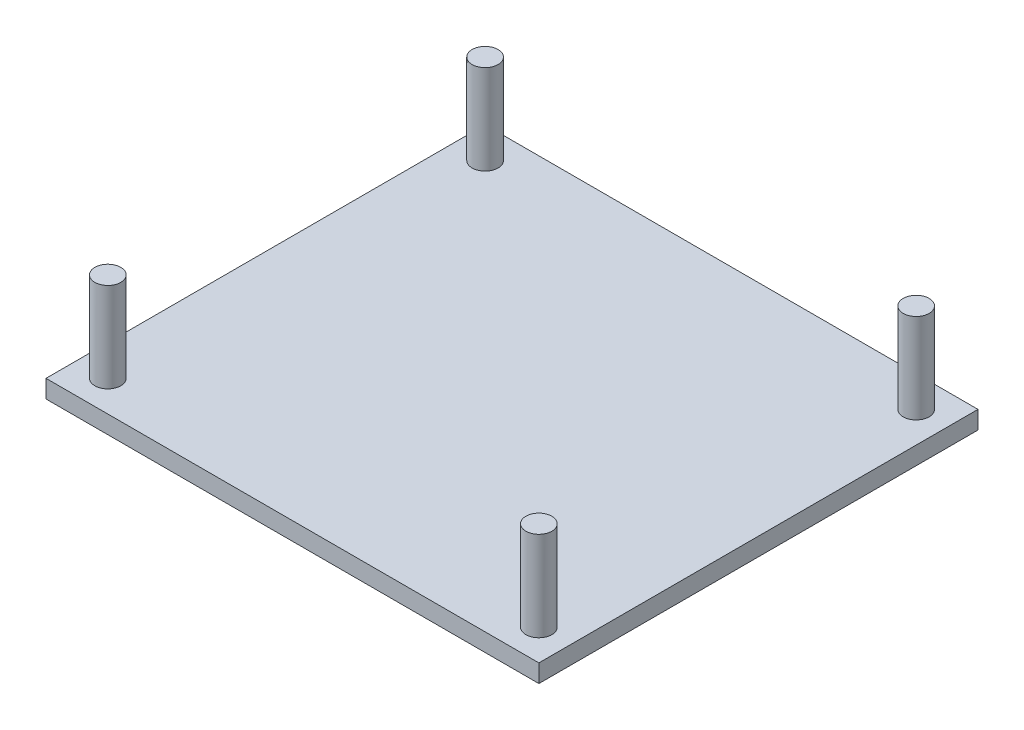
SolidWorks part; units mm, degrees
ref_plane "Front Plane" through (0, 0, 0) normal (0, 0, 1) x (1, 0, 0)
ref_plane "Top Plane" through (0, 0, 0) normal (0, 1, 0) x (1, 0, 0)
ref_plane "Right Plane" through (0, 0, 0) normal (1, 0, 0) x (0, 0, -1)
sketch "Sketch1" plane through (0, 0, 0) normal (0, 1, 0) x (1, 0, 0)
  line L1 (0, 0) -> (55, 0)
  line L2 (0, 0) -> (0, 49)
  line L3 (0, 49) -> (55, 49)
  line L4 (55, 0) -> (55, 49)
  dimension "D1" = 49
  dimension "D2" = 55
extrude "Boss-Extrude1" add sketch "Sketch1" against normal blind 2
sketch "Sketch2" plane through (0, 0, 0) normal (0, 1, 0) x (1, 0, 0)
  line L0 (-19.6794, 24.5) -> (76.4972, 24.5) construction
  line L1 (55, 49) -> (0, 49) construction
  line L2 (0, 0) -> (55, 0) construction
  line L3 (0, 49) -> (0, 0) construction
  line L4 (55, 0) -> (55, 49) construction
  circle A0 centre (3.45, 3.45) radius 1.45
  circle A1 centre (51.55, 3.45) radius 1.45
  circle A2 centre (51.55, 45.55) radius 1.45
  circle A3 centre (3.45, 45.55) radius 1.45
  dimension "D2" = 2.9
  dimension "D3" = 3.45
  dimension "D4" = 3.45
  dimension "D5" = 2.9
  dimension "D6" = 3.45
  dimension "D7" = 3.45
  dimension "D1" = 24.5
extrude "Boss-Extrude2" add sketch "Sketch2" along normal blind 10
